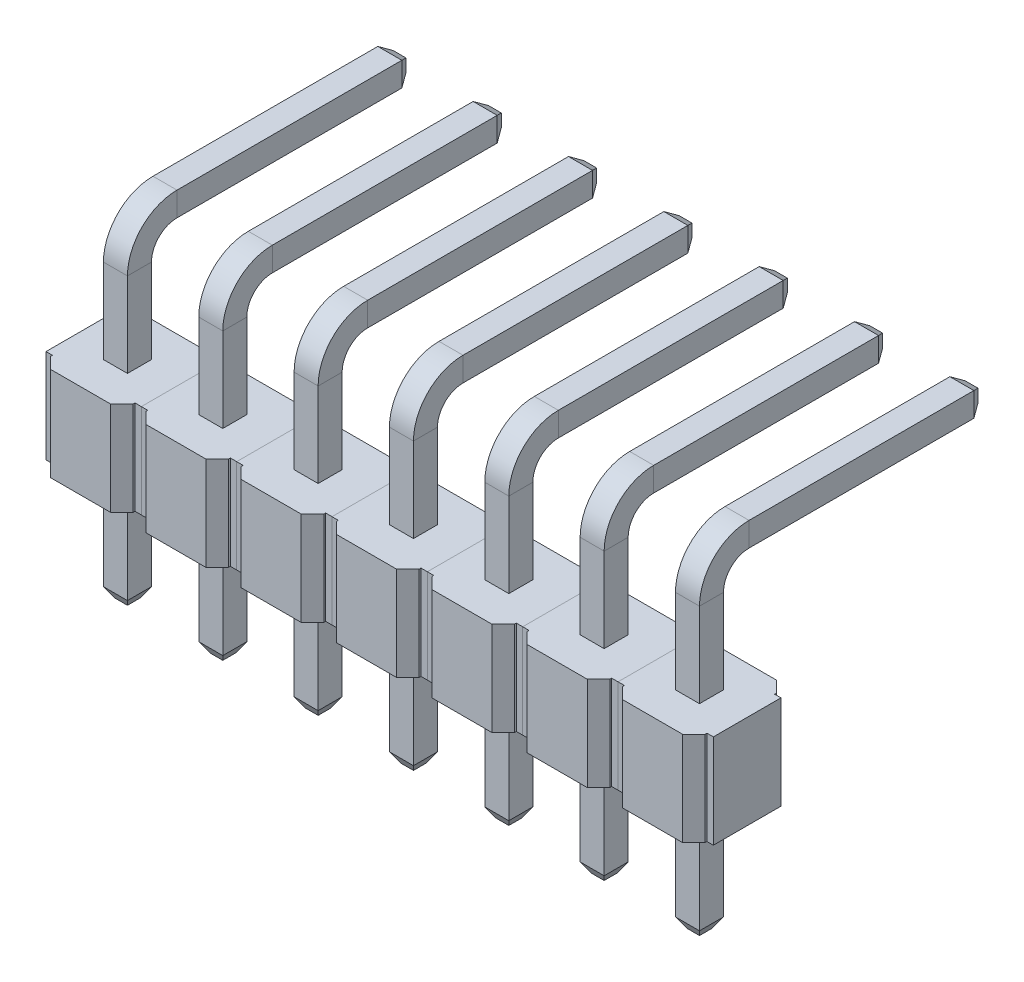
SolidWorks part; units mm, degrees
ref_plane "Front" through (0, 0, 0) normal (0, 0, 1) x (1, 0, 0)
ref_plane "Top" through (0, 0, 0) normal (0, 1, 0) x (1, 0, 0)
ref_plane "Right" through (0, 0, 0) normal (1, 0, 0) x (0, 0, -1)
sketch "Эскиз2" plane through (0, 0, 0) normal (1, 0, 0) x (0, 0, -1)
  line L0 (0, 0) -> (0, -3)
  line L1 (0, 0) -> (0, 4.75)
  line L2 (1, 5.75) -> (7.25, 5.75)
  arc A0 (1, 5.75) -> (0, 4.75) centre (1, 4.75) ccw
  point P7 (0, 5.75)
  dimension "D4" = 1
  dimension "D1" = 3
  dimension "D2" = 5.75
  dimension "D3" = 7.25
sketch "Эскиз3" plane through (0, 0, 0) normal (0, 1, 0) x (1, 0, 0)
  line L1 (-0.32, -0.32) -> (0.32, -0.32)
  line L2 (-0.32, -0.32) -> (-0.32, 0.32)
  line L3 (-0.32, 0.32) -> (0.32, 0.32)
  line L4 (0.32, -0.32) -> (0.32, 0.32)
  line L5 (-0.32, -0.32) -> (0.32, 0.32) construction
  line L6 (-0.32, 0.32) -> (0.32, -0.32) construction
  point P0 (0, 0)
sweep "По траектории1" add profiles "Эскиз3" path "Эскиз2"
chamfer "Фаска1" distance 0.15 angle 60 8 edges at (0, -3, -0.32) (-0.32, -3, 0) (0, -3, 0.32) (0.32, -3, 0) (0, 6.07, -7.25) (-0.32, 5.75, -7.25) (0, 5.43, -7.25) (0.32, 5.75, -7.25)
sketch "Эскиз4" plane through (0, 0, 0) normal (0, 1, 0) x (1, 0, 0)
  line L0 (-1.1, 0.9) -> (-1.1, 1.25)
  line L1 (-1.1, -1.25) -> (1.1, -1.25)
  line L2 (-1.1, -1.25) -> (-1.1, -0.9)
  line L3 (-1.1, 1.25) -> (1.1, 1.25)
  line L4 (1.1, -1.25) -> (1.1, -0.9)
  line L5 (-1.1, -1.25) -> (1.1, 1.25) construction
  line L6 (-1.1, 1.25) -> (1.1, -1.25) construction
  line L7 (-1.27, -0.9) -> (-1.1, -0.9)
  line L8 (-1.27, -0.9) -> (-1.27, 0.9)
  line L9 (-1.27, 0.9) -> (-1.1, 0.9)
  line L10 (1.27, -0.9) -> (1.27, 0.9)
  line L11 (-1.27, -0.9) -> (1.27, 0.9) construction
  line L12 (-1.27, 0.9) -> (1.27, -0.9) construction
  line L13 (1.1, 0.9) -> (1.1, 1.25)
  line L14 (1.1, -0.9) -> (1.27, -0.9)
  line L15 (1.1, 0.9) -> (1.27, 0.9)
  point P0 (0, 0)
  point P5 (0, 0)
  dimension "D1" = 2.2
  dimension "D2" = 2.5
  dimension "D3" = 1.8
  dimension "D4" = 2.54
extrude "Бобышка-Вытянуть1" add sketch "Эскиз4" along normal blind 2.5 separate body
chamfer "Фаска2" distance 0.3 angle 45 4 edges at (-1.1, 1.25, -1.25) (1.1, 1.25, -1.25) (-1.1, 1.25, 1.25) (1.1, 1.25, 1.25)
pattern_linear "Линейный массив1" count 7 spacing 2.54 along (-1, 0, 0) of bodies 102 101
equation "\"D2@Эскиз2\"=6.07-0.64/2"
equation "\"D3@Эскиз2\"=6+2.5/2"
